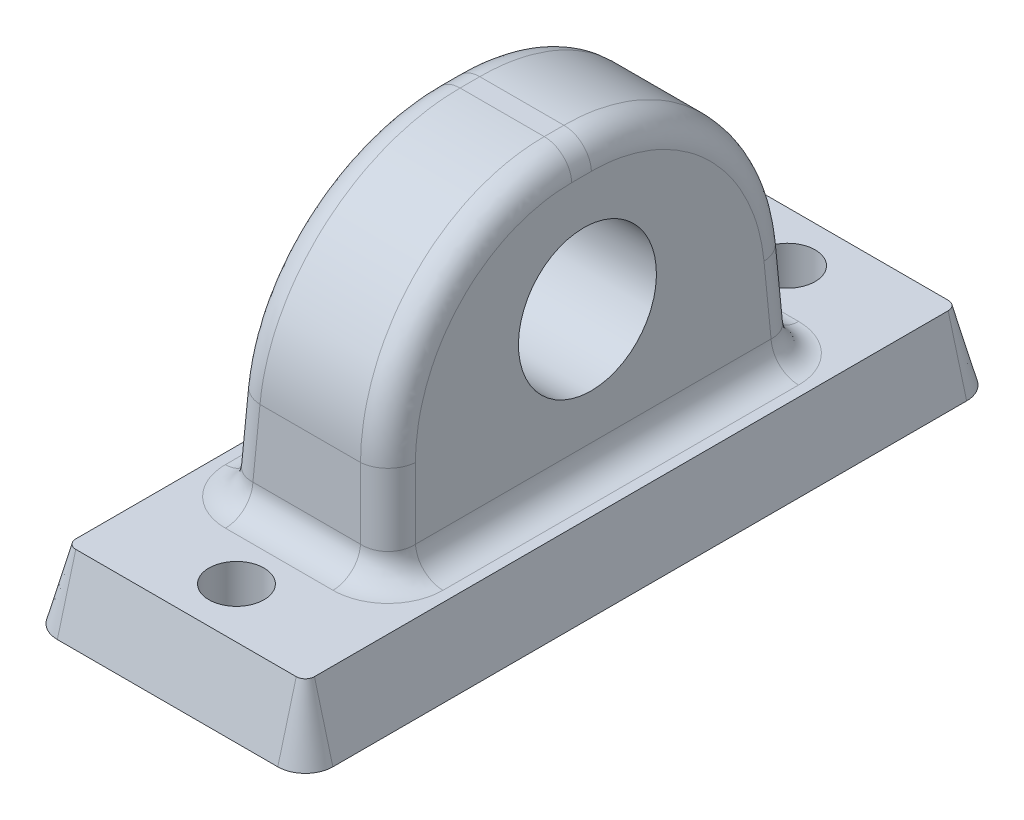
SolidWorks part; units mm, degrees
ref_plane "Front Plane" through (0, 0, 0) normal (0, 0, 1) x (1, 0, 0)
ref_plane "Top Plane" through (0, 0, 0) normal (0, 1, 0) x (1, 0, 0)
ref_plane "Right Plane" through (0, 0, 0) normal (1, 0, 0) x (0, 0, -1)
sketch "Sketch1" plane through (0, 0, 0) normal (0, 1, 0) x (1, 0, 0)
  line L1 (-8, -25) -> (8, -25)
  line L2 (-10, -23) -> (-10, 23)
  line L3 (-8, 25) -> (8, 25)
  line L4 (10, -23) -> (10, 23)
  arc A0 (8, 25) -> (10, 23) centre (8, 23) cw
  arc A1 (-8, -25) -> (-10, -23) centre (-8, -23) cw
  arc A2 (8, -25) -> (10, -23) centre (8, -23) ccw
  arc A3 (-10, 23) -> (-8, 25) centre (-8, 23) cw
  arc A4 (8, 25) -> (10, 23) centre (8, 23) cw
  arc A5 (8, 25) -> (10, 23) centre (8, 23) cw
  arc A6 (8, 25) -> (10, 23) centre (8, 23) cw
  arc A7 (8, 25) -> (10, 23) centre (8, 23) cw
  point P0 (0, 0)
  dimension "D3" = 2
  dimension "D4" = 2
  dimension "D5" = 2
  dimension "D6" = 2
  dimension "D7" = 2
extrude "Boss-Extrude1" add sketch "Sketch1" along normal blind 5 draft 15 contours L2 A3 L3 A7 L4 A2 L1 A1
sketch "Sketch2" plane through (0, 5, 0) normal (0, 1, 0) x (1, 0, 0)
  line L0 (0, 23.6603) -> (0, -23.6603) construction
  line L1 (-8, 23.6603) -> (8, 23.6603) construction
  line L2 (-8, -23.6603) -> (8, -23.6603) construction
  line L3 (-8.6603, 0) -> (8.6603, 0) construction
  line L4 (-8.6603, -23) -> (-8.6603, 23) construction
  line L5 (8.6603, -23) -> (8.6603, 23) construction
  circle A0 centre (0, 20) radius 2
  circle A1 centre (0, -20) radius 2
  point P12 (0, 20)
  point P13 (0, -20)
  dimension "D3" = 4
  dimension "D4" = 4
  dimension "D1" = 20
  dimension "D2" = 20
extrude "Cut-Extrude1" cut sketch "Sketch2" against normal blind 5
sketch "Sketch3" plane through (0, 5, 0) normal (0, 1, 0) x (1, 0, 0)
  line L1 (-6, -15) -> (6, -15)
  line L2 (-6, -15) -> (-6, 15)
  line L3 (-6, 15) -> (6, 15)
  line L4 (6, -15) -> (6, 15)
  line L5 (-6, -15) -> (6, 15) construction
  line L6 (-6, 15) -> (6, -15) construction
  point P0 (0, 0)
  dimension "D1" = 12
  dimension "D2" = 30
extrude "Boss-Extrude2" add sketch "Sketch3" along normal blind 20 draft 3
fillet "Fillet1" radius 13.95 2 edges at (0, 25, -13.9518) (0, 25, 13.9518)
fillet "Fillet2" radius 2 14 edges at (0, 5, -15) (-5.1526, 21.169, 10.3163) (-5.8223, 8.39, 14.8223) (-6, 5, 0) (-5.8223, 8.39, -14.8223) (-4.9518, 25, 0) (-5.1526, 21.169, -10.3163) (6, 5, 0) (5.8223, 8.39, 14.8223) (5.1526, 21.169, 10.3163) (4.9518, 25, 0) (5.1526, 21.169, -10.3163) (5.8223, 8.39, -14.8223) (0, 5, 15)
ref_plane "Plane1" through (6, 0, 0) normal (1, 0, 0) x (0, 0, -1)
sketch "Sketch4" plane through (6, 0, 0) normal (1, 0, 0) x (0, 0, -1)
  line L0 (0, 23.1047) -> (0, 6.8953) construction
  line L1 (0.7138, 23.1047) -> (-0.7138, 23.1047) construction
  line L2 (-12.9034, 6.8953) -> (12.9034, 6.8953) construction
  circle A0 centre (0, 15) radius 5
  dimension "D1" = 10
extrude "Cut-Extrude2" cut sketch "Sketch4" against normal blind 24
sketch "Sketch6" plane through (-6.2449, 0.3273, 0) normal (-0.9986, 0.0523, 0) x (0, 0, 1)
  point P12 (0, 9.686)
sketch "Sketch7" plane through (6.2449, 0.3273, 0) normal (0.9986, 0.0523, 0) x (0, 0, -1)
  point P12 (0, 9.686)
